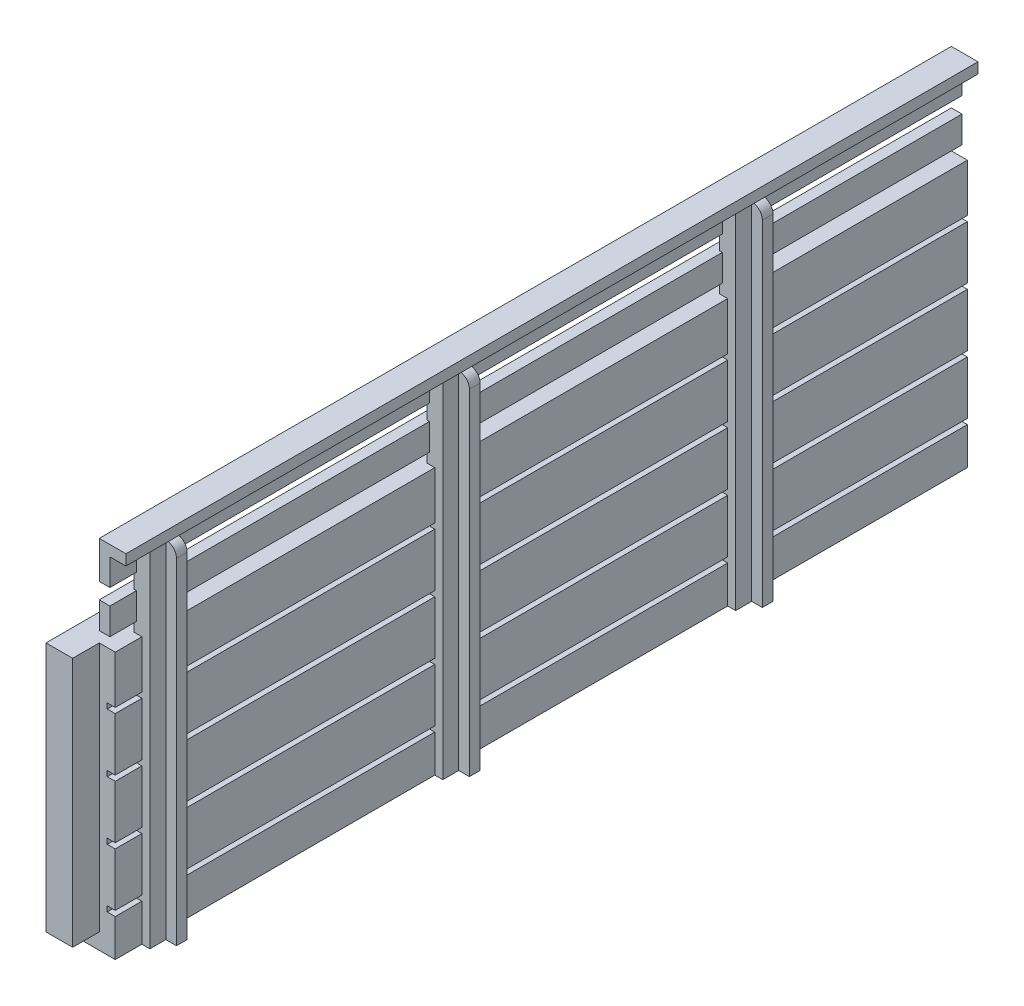
SolidWorks part; units mm, degrees
ref_plane "Front Plane" through (0, 0, 0) normal (0, 0, 1) x (1, 0, 0)
ref_plane "Top Plane" through (0, 0, 0) normal (0, 1, 0) x (1, 0, 0)
ref_plane "Right Plane" through (0, 0, 0) normal (1, 0, 0) x (0, 0, -1)
sketch "Sketch1" plane through (0, 0, 0) normal (1, 0, 0) x (0, 0, -1)
  line L1 (-80, 25) -> (80, 25)
  line L2 (-80, 25) -> (-80, -25)
  line L3 (-80, -25) -> (80, -25)
  line L4 (80, 25) -> (80, -25)
  line L5 (-80, 25) -> (80, -25) construction
  line L6 (-80, -25) -> (80, 25) construction
  point P0 (0, 0)
  dimension "D1" = 160
  dimension "D2" = 50
extrude "Boss-Extrude1" add sketch "Sketch1" along normal blind 3
sketch "Sketch2" plane through (3, 0, 0) normal (1, 0, 0) x (0, 0, -1)
  line L0 (-80, 25) -> (-80, -25) construction
  line L1 (-80, -17) -> (80, -17)
  line L2 (-80, -17) -> (-80, -18)
  line L3 (-80, -18) -> (80, -18)
  line L4 (80, -17) -> (80, -18)
  line L5 (80, -25) -> (80, 25) construction
  line L6 (-80, -25) -> (80, -25) construction
  line L7 (80, 25) -> (-80, 25) construction
  line L8 (-80, -6) -> (80, -6)
  line L9 (-80, -6) -> (-80, -7)
  line L10 (-80, -7) -> (80, -7)
  line L11 (80, -6) -> (80, -7)
  line L12 (-80, 5) -> (80, 5)
  line L13 (-80, 5) -> (-80, 4)
  line L14 (-80, 4) -> (80, 4)
  line L15 (80, 5) -> (80, 4)
  line L16 (-80, 16) -> (80, 16)
  line L17 (-80, 16) -> (-80, 15)
  line L18 (-80, 15) -> (80, 15)
  line L19 (80, 16) -> (80, 15)
  dimension "D1" = 1
  dimension "D2" = 7
  dimension "D3" = 1
  dimension "D4" = 10
  dimension "D5" = 1
  dimension "D6" = 10
  dimension "D7" = 1
  dimension "D8" = 10
  dimension "D9" = 9
extrude "Cut-Extrude1" cut sketch "Sketch2" against normal blind 1.5
sketch "Sketch3" plane through (3, 0, 0) normal (1, 0, 0) x (0, 0, -1)
  line L6 (-70, -25) -> (-75, -25)
  line L7 (-80, -25) -> (80, -25) construction
  line L8 (40, -25) -> (35, -25)
  line L9 (40, -25) -> (40, 40)
  line L10 (40, 40) -> (35, 40)
  line L11 (35, -25) -> (35, 40)
  line L12 (80, -25) -> (80, -18) construction
  line L13 (-70, -25) -> (-70, 40)
  line L14 (-15, -25) -> (-20, -25)
  line L15 (-15, -25) -> (-15, 40)
  line L16 (-15, 40) -> (-20, 40)
  line L17 (-20, -25) -> (-20, 40)
  line L22 (-70, 40) -> (-75, 40)
  line L23 (-75, -25) -> (-75, 40)
  dimension "D1" = 65
  dimension "D2" = 40
  dimension "D3" = 5
  dimension "D4" = 5
  dimension "D5" = 65
  dimension "D6" = 50
  dimension "D7" = 5
  dimension "D8" = 50
  dimension "D9" = 65
extrude "Boss-Extrude2" add sketch "Sketch3" along normal mid plane 3
sketch "Sketch4" plane through (4.5, 0, 0) normal (1, 0, 0) x (0, 0, -1)
  line L0 (40, 40) -> (35, 40) construction
  line L1 (40, -25) -> (38, -25)
  line L2 (40, -25) -> (40, 40)
  line L3 (40, 40) -> (38, 40)
  line L4 (38, -25) -> (38, 40)
  line L5 (-15, 40) -> (-20, 40) construction
  line L6 (-15, -25) -> (-17, -25)
  line L7 (-15, -25) -> (-15, 40)
  line L8 (-15, 40) -> (-17, 40)
  line L9 (-17, -25) -> (-17, 40)
  line L16 (-70, 40) -> (-75, 40) construction
  line L17 (-70, -25) -> (-72, -25)
  line L18 (-70, -25) -> (-70, 40)
  line L19 (-70, 40) -> (-72, 40)
  line L20 (-72, -25) -> (-72, 40)
  dimension "D1" = 2
  dimension "D2" = 2
  dimension "D3" = 2
extrude "Boss-Extrude3" add sketch "Sketch4" along normal blind 2
fillet "Fillet1" radius 2 3 edges at (6.5, 40, 71) (6.5, 40, 16) (6.5, 40, -39)
sketch "Sketch5" plane through (0, 0, 0) normal (-1, 0, 0) x (0, 0, 1)
  line L5 (80, -25) -> (80, 70.4394) construction
  line L10 (-80, -25) -> (-80, 70.4394) construction
  line L15 (-80, 25) -> (80, 25) construction
  line L16 (-80, 27) -> (80, 27)
  line L17 (-80, 27) -> (-80, 32)
  line L18 (-80, 32) -> (80, 32)
  line L19 (80, 27) -> (80, 32)
  line L21 (-80, 40) -> (80, 40)
  line L22 (-80, 40) -> (-80, 35)
  line L23 (-80, 35) -> (80, 35)
  line L24 (80, 40) -> (80, 35)
  dimension "D2" = 2
  dimension "D3" = 5
  dimension "D4" = 5
  dimension "D5" = 3
extrude "Boss-Extrude4" add sketch "Sketch5" against normal blind 2 separate body
sketch "Sketch7" plane through (0, 0, 0) normal (-1, 0, 0) x (0, 0, 1)
  line L0 (80, 25) -> (80, -25) construction
  line L1 (-80, -25) -> (80, -25)
  line L2 (-80, -25) -> (-80, -22)
  line L3 (-80, -22) -> (80, -22)
  line L4 (80, -25) -> (80, -22)
  dimension "D1" = 3
extrude "Boss-Extrude5" add sketch "Sketch7" along normal blind 5
sketch "Sketch8" plane through (0, 40, 0) normal (0, 1, 0) x (1, 0, 0)
  line L0 (2, -80) -> (0, -80) construction
  line L1 (0, 80) -> (5, 80)
  line L2 (0, 80) -> (0, -80)
  line L3 (0, -80) -> (5, -80)
  line L4 (5, 80) -> (5, -80)
  dimension "D1" = 5
extrude "Boss-Extrude6" add sketch "Sketch8" along normal blind 2
sketch "Sketch11" plane through (0, 0, 0) normal (-1, 0, 0) x (0, 0, 1)
  line L7 (80, -22) -> (-80, -22) construction
  line L8 (75, -22) -> (85, -22)
  line L9 (75, -22) -> (75, 25)
  line L10 (75, 25) -> (85, 25)
  line L11 (85, -22) -> (85, 25)
  line L12 (80, 25) -> (80, -22) construction
  dimension "D1" = 10
  dimension "D2" = 5
extrude "Boss-Extrude7" add sketch "Sketch11" along normal blind 5
sketch "Sketch10" plane through (0, 0, 84.9948) normal (0, 0, 1) x (1, 0, 0)
  line L4 (2, 42) -> (2, 40)
  line L5 (2, 40) -> (5, 40)
  line L6 (5, 40) -> (5, 42)
  line L7 (5, 42) -> (2, 42)
  line L8 (2, 42) -> (2, 40)
  line L9 (2, 40) -> (5, 40)
  line L10 (5, 40) -> (5, 42)
  line L11 (5, 42) -> (2, 42)
  dimension "D1" = 0
